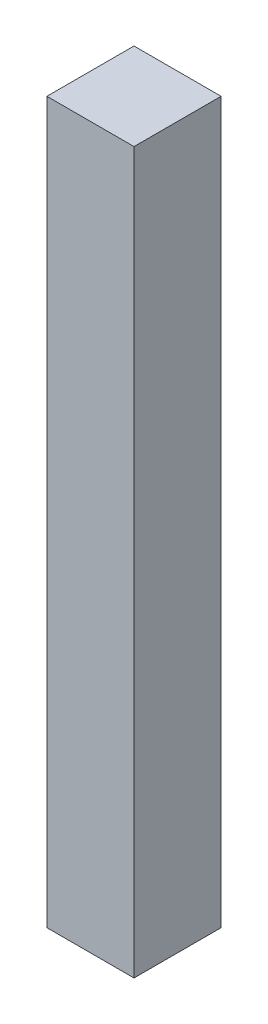
SolidWorks part; units mm, degrees
ref_plane "Front Plane" through (0, 0, 0) normal (0, 0, 1) x (1, 0, 0)
ref_plane "Top Plane" through (0, 0, 0) normal (0, 1, 0) x (1, 0, 0)
ref_plane "Right Plane" through (0, 0, 0) normal (1, 0, 0) x (0, 0, -1)
sketch "Sketch1" plane through (0, 0, 0) normal (0, 1, 0) x (1, 0, 0)
  line L1 (-39.8355, 18.6136) -> (-14.4355, 18.6136)
  line L2 (-39.8355, 18.6136) -> (-39.8355, -6.7864)
  line L3 (-39.8355, -6.7864) -> (-14.4355, -6.7864)
  line L4 (-14.4355, 18.6136) -> (-14.4355, -6.7864)
  dimension "D1" = 25.4
  dimension "D2" = 25.4
extrude "Boss-Extrude1" add sketch "Sketch1" along normal blind 210
